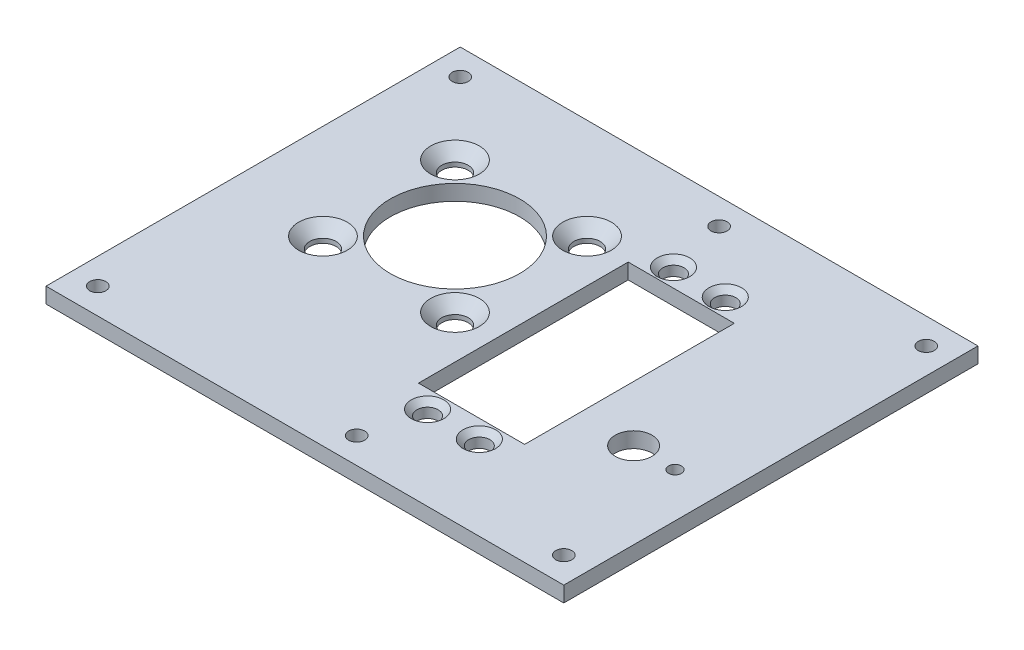
SolidWorks part; units mm, degrees
ref_plane "Płaszczyzna przednia" through (0, 0, 0) normal (0, 0, 1) x (1, 0, 0)
ref_plane "Płaszczyzna górna" through (0, 0, 0) normal (0, 1, 0) x (1, 0, 0)
ref_plane "Płaszczyzna prawa" through (0, 0, 0) normal (1, 0, 0) x (0, 0, -1)
sketch "Szkic1" plane through (0, 0, 0) normal (0, 1, 0) x (1, 0, 0)
  line L6 (-20.2688, 11.7569) -> (5.2312, -13.7431) construction
  line L11 (-38.6633, 31.161) -> (61.3367, 31.161)
  line L12 (-38.6633, 31.161) -> (-38.6633, -48.839)
  line L13 (-38.6633, -48.839) -> (61.3367, -48.839)
  line L14 (61.3367, 31.161) -> (61.3367, -48.839)
  line L15 (-20.2688, -13.7431) -> (5.2312, 11.7569) construction
  line L17 (13.5251, 11.411) -> (34.0251, 11.411)
  line L18 (13.5251, 11.411) -> (13.5251, -29.089)
  line L23 (13.5251, -29.089) -> (34.0251, -29.089)
  line L24 (34.0251, 11.411) -> (34.0251, -29.089)
  circle A0 centre (-7.5188, -0.9931) radius 12.5
  circle A2 centre (-20.2688, 11.7569) radius 2.55
  circle A3 centre (5.2312, 11.7569) radius 2.55
  circle A4 centre (5.2312, -13.7431) radius 2.55
  circle A5 centre (-20.2688, -13.7431) radius 2.55
  circle A6 centre (18.7751, 14.911) radius 2.05
  circle A7 centre (28.7751, 14.911) radius 2.05
  circle A8 centre (18.7751, -32.589) radius 2.05
  circle A9 centre (28.7751, -32.589) radius 2.05
  circle A10 centre (23.7751, -18.789) radius 0.5
  circle A11 centre (-7.5188, -0.9931) radius 0.5
  circle A12 centre (44.7751, -18.789) radius 3.55
  circle A13 centre (44.7751, -18.789) radius 0.5
  circle A14 centre (-33.6633, 26.161) radius 1.55
  circle A15 centre (56.3367, 26.161) radius 1.55
  circle A16 centre (56.3367, -43.839) radius 1.55
  circle A17 centre (-33.6633, -43.839) radius 1.55
  circle A18 centre (16.3367, 26.161) radius 1.55
  circle A19 centre (16.3367, -43.839) radius 1.55
  circle A20 centre (52.7751, -18.789) radius 1.25
  point P18 (23.7751, -29.089)
  point P22 (23.7751, 11.411)
  point P27 (11.3367, -8.839)
  point P47 (52.7751, -18.789)
  dimension "D3" = 10.3
  dimension "D5" = 3.5
  dimension "D13" = 36
  dimension "D18" = 19.75
  dimension "D20" = 5.1
  dimension "D22" = 25
  dimension "D23" = 7.1
  dimension "D24" = 4.1
  dimension "D25" = 47.5
  dimension "D28" = 8
  dimension "D26" = 37.5616
  dimension "D1" = 100
  dimension "D2" = 80
  dimension "D4" = 10.25
  dimension "D6" = 3.5
  dimension "D7" = 5
  dimension "D8" = 5
  dimension "D9" = 3.5
  dimension "D10" = 3.5
  dimension "D11" = 5
  dimension "D12" = 5
  dimension "D14" = 21
  dimension "D15" = 40.5
  dimension "D16" = 20.5
  dimension "D17" = 10.3
  dimension "D19" = 19.75
  dimension "D21" = 25.5
  dimension "D27" = 30.05
extrude "Dodanie-wyciągnięcie1" add sketch "Szkic1" along normal blind 3 contours L14 L11 L12 L13 A12 A9 A8 A7 A6 A5 A4 A3 A2 A0 L17 L24 L23 L18
sketch "Sketch1" plane through (0, 0, 0) normal (0, 1, 0) x (1, 0, 0)
  point P0 (-20.2688, -13.7431)
  point P3 (5.2312, -13.7431)
  point P6 (5.2312, 11.7569)
  point P9 (-20.2688, 11.7569)
sketch "Sketch3" plane through (0, 3, 0) normal (0, 1, 0) x (1, 0, 0)
  point P0 (-20.2688, -13.7431)
  point P3 (5.2312, -13.7431)
  point P6 (5.2312, 11.7569)
  point P9 (-20.2688, 11.7569)
hole_wizard "CSK for M4 Countersunk Flat Head Screw1" positions "Sketch3" profile "Sketch4" countersink size "M4" standard "ISO" end condition through all
sketch "Sketch4" plane through (-20.2688, 3, 13.7431) normal (1, 0, 0) x (0, 0, 1)
  line L0 (0, 0) -> (0, 3)
  line L1 (0, 3) -> (2.25, 3)
  line L2 (2.25, 3) -> (2.25, 2.45)
  line L3 (2.25, 2.45) -> (4.7, 0)
  line L5 (4.7, 0) -> (0, 0)
  line L6 (-2.25, 2.45) -> (-4.7, 0) construction
  line L11 (0, -6.35) -> (0, 107.95) construction
  dimension "Thru Hole Dia." = 4.5
  dimension "Thru Hole Depth" = 3
  dimension "Near C'Sink Dia." = 9.4
  dimension "Near C'Sink Angle" = 90
sketch "Sketch5" plane through (0, 3, 0) normal (0, 1, 0) x (1, 0, 0)
  point P0 (18.7751, 14.911)
  point P3 (28.7751, 14.911)
  point P6 (18.7751, -32.589)
  point P9 (28.7751, -32.589)
hole_wizard "CSK for M3 Countersunk Flat Head Screw1" positions "Sketch5" profile "Sketch6" countersink size "M3" standard "ISO" end condition through all
sketch "Sketch6" plane through (18.7751, 3, -14.911) normal (1, 0, 0) x (0, 0, 1)
  line L0 (0, 0) -> (0, 3)
  line L1 (0, 3) -> (1.7, 3)
  line L2 (1.7, 3) -> (1.7, 1.45)
  line L3 (1.7, 1.45) -> (3.15, 0)
  line L5 (3.15, 0) -> (0, 0)
  line L6 (-1.7, 1.45) -> (-3.15, 0) construction
  line L11 (0, -6.35) -> (0, 107.95) construction
  dimension "Thru Hole Dia." = 3.4
  dimension "Thru Hole Depth" = 3
  dimension "Near C'Sink Dia." = 6.3
  dimension "Near C'Sink Angle" = 90
